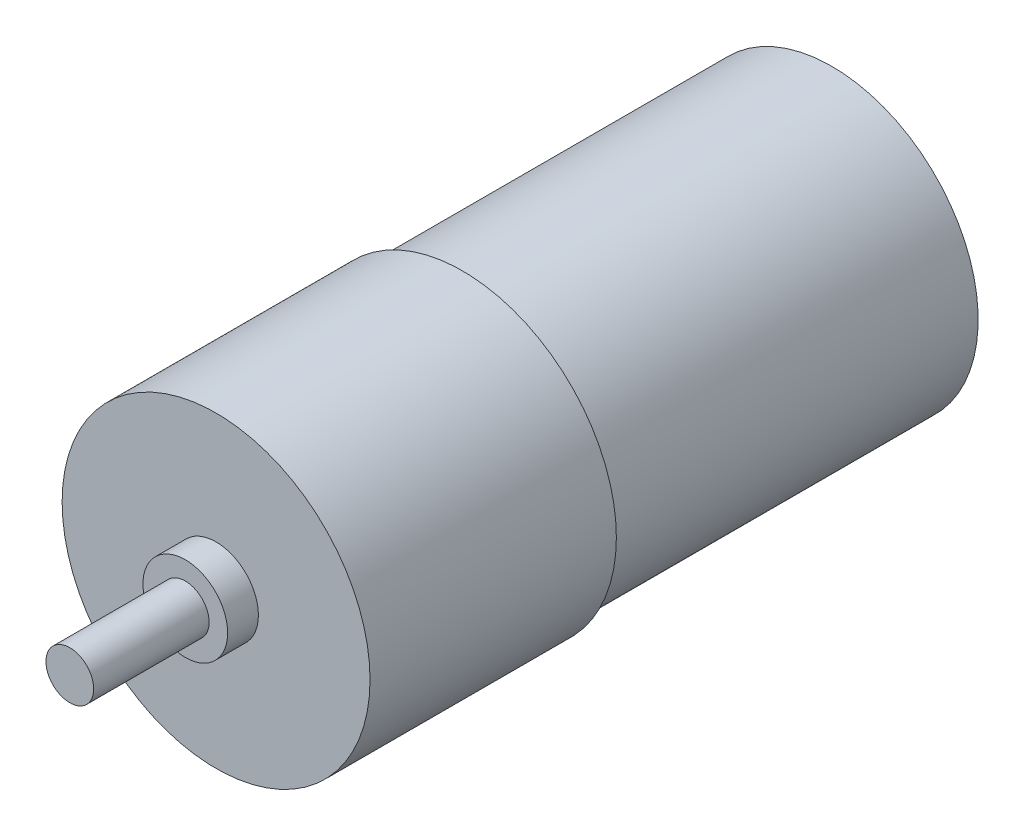
SolidWorks part; units mm, degrees
ref_plane "Front Plane" through (0, 0, 0) normal (0, 0, 1) x (1, 0, 0)
ref_plane "Top Plane" through (0, 0, 0) normal (0, 1, 0) x (1, 0, 0)
ref_plane "Right Plane" through (0, 0, 0) normal (1, 0, 0) x (0, 0, -1)
sketch "Sketch1" plane through (0, 0, 0) normal (0, 0, 1) x (1, 0, 0)
  circle A0 centre (0, 0) radius 12.7
  dimension "D1" = 25.4
extrude "Boss-Extrude1" add sketch "Sketch1" along normal blind 50.8
sketch "Sketch2" plane through (0, 0, 50.8) normal (0, 0, 1) x (1, 0, 0)
  circle A0 centre (0, 0) radius 3.4925
  dimension "D1" = 6.985
extrude "Boss-Extrude2" add sketch "Sketch2" along normal blind 2.54 contours A0
sketch "Sketch3" plane through (0, 0, 53.34) normal (0, 0, 1) x (1, 0, 0)
  circle A0 centre (0, 0) radius 1.9685
  dimension "D1" = 3.937
extrude "Boss-Extrude3" add sketch "Sketch3" along normal blind 9.525
sketch "Sketch4" plane through (0, 0, 0) normal (0, 0, -1) x (-1, 0, 0)
  circle A0 centre (0, 0) radius 12.065
  dimension "D1" = 24.13
extrude "Cut-Extrude1" cut sketch "Sketch4" against normal blind 30.48 flip side to cut
